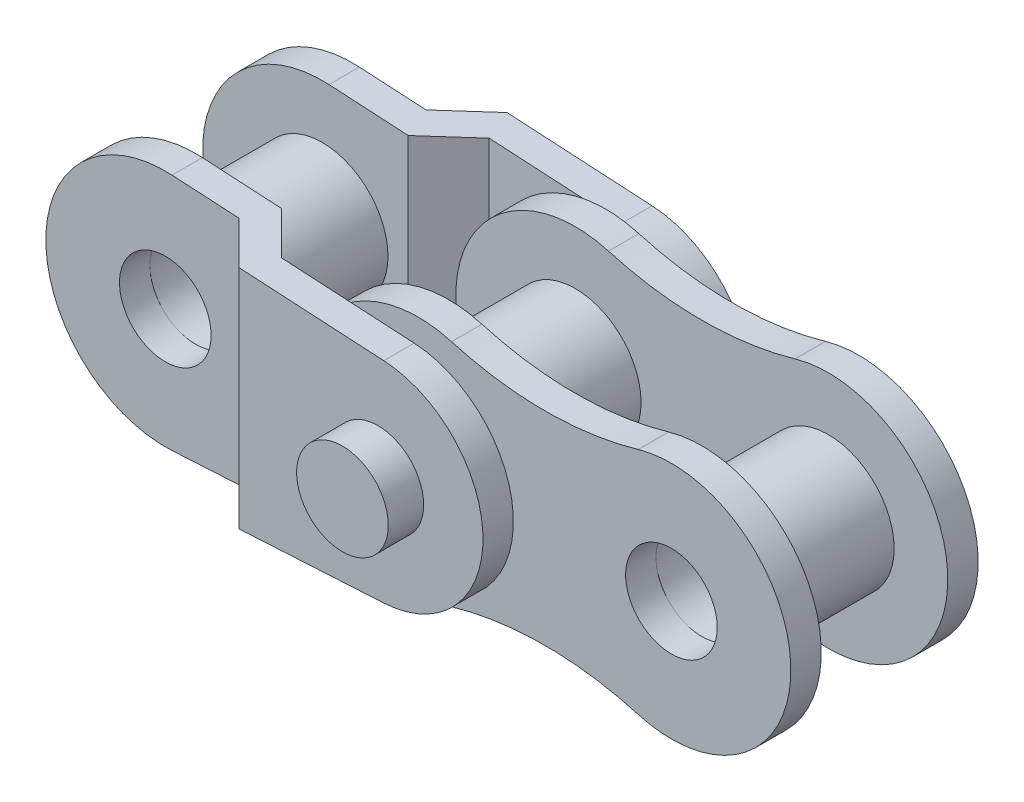
SolidWorks part; units mm, degrees
ref_plane "Front Plane" through (0, 0, 0) normal (0, 0, 1) x (1, 0, 0)
ref_plane "Top Plane" through (0, 0, 0) normal (0, 1, 0) x (1, 0, 0)
ref_plane "Right Plane" through (0, 0, 0) normal (1, 0, 0) x (0, 0, -1)
sketch "Sketch1" plane through (0, 0, 0) normal (0, 0, 1) x (1, 0, 0)
  line L0 (-3.175, 0) -> (3.175, 0) construction
  line L1 (-3.175, 2.9972) -> (-3.175, -2.9972) construction
  line L2 (0, -2.5476) -> (0, 2.5476) construction
  circle A0 centre (-3.175, 0) radius 1.651
  circle A1 centre (3.175, 0) radius 1.651
  circle A2 centre (-3.175, 0) radius 1.1493
  circle A3 centre (3.175, 0) radius 1.1493
  arc A4 (-2.3429, 2.8794) -> (-2.3429, -2.8794) centre (-3.175, 0) ccw
  arc A5 (2.3429, -2.8794) -> (2.3429, 2.8794) centre (3.175, 0) ccw
  arc A6 (-2.3429, 2.8794) -> (2.3429, 2.8794) centre (0, 10.9864) ccw
  arc A7 (-2.3429, -2.8794) -> (2.3429, -2.8794) centre (0, -10.9864) cw
  dimension "Roller Dia" = 3.302
  dimension "Pin Dia" = 2.2987
  dimension "Pitch" = 6.35
  dimension "H" = 5.9944
  dimension "D2" = 5.0952
sketch "Sketch2" plane through (0, 0, 0) normal (0, 1, 0) x (1, 0, 0)
  line L0 (0, 1.5875) -> (0, -1.5875) construction
  point P2 (0, -2.3495)
  point P4 (0, 2.3495)
  point P5 (0, 2.6035)
  point P6 (0, 3.3655)
  dimension "W" = 3.175
  dimension "T" = 0.762
  dimension "D1" = 0.762
  dimension "D2" = 0.762
  dimension "D3" = 0.254
ref_plane "Plane1" through (0, 0, 1.5875) normal (0, 0, 1) x (1, 0, 0)
ref_plane "Plane2" through (0, 0, -2.6035) normal (0, 0, 1) x (1, 0, 0)
sketch "Sketch5" plane through (0, 0, 1.5875) normal (0, 0, 1) x (1, 0, 0)
  arc A0 (-2.3429, 2.8794) -> (-2.3429, -2.8794) centre (-3.175, 0) ccw construction
  arc A1 (-2.3429, 2.8794) -> (2.3429, 2.8794) centre (0, 10.9864) ccw construction
  circle A2 centre (-3.175, 0) radius 1.1493 construction
  arc A3 (2.3429, -2.8794) -> (2.3429, 2.8794) centre (3.175, 0) ccw construction
  circle A4 centre (3.175, 0) radius 1.1493 construction
  arc A5 (2.3429, -2.8794) -> (-2.3429, -2.8794) centre (0, -10.9864) ccw construction
  arc A6 (-2.3429, 2.8794) -> (-2.3429, -2.8794) centre (-3.175, 0) ccw
  arc A7 (-2.3429, 2.8794) -> (2.3429, 2.8794) centre (0, 10.9864) ccw
  circle A8 centre (-3.175, 0) radius 1.1493
  arc A9 (2.3429, -2.8794) -> (2.3429, 2.8794) centre (3.175, 0) ccw
  circle A10 centre (3.175, 0) radius 1.1493
  arc A11 (2.3429, -2.8794) -> (-2.3429, -2.8794) centre (0, -10.9864) ccw
sketch "Sketch7" plane through (0, 0, -2.6035) normal (0, 0, 1) x (1, 0, 0)
  line L0 (3.175, 2.6375) -> (3.175, -2.6375) construction
  circle A0 centre (3.175, 0) radius 2.6375
  circle A1 centre (-3.175, 0) radius 1.1493 construction
  arc A2 (2.3429, -2.8794) -> (2.3429, 2.8794) centre (3.175, 0) ccw construction
  circle A8 centre (3.175, 0) radius 1.1493
  dimension "D2" = 5.2751
sketch "Sketch4" plane through (0, 0, 0) normal (0, 0, 1) x (1, 0, 0)
  circle A0 centre (-3.175, 0) radius 1.651 construction
  circle A1 centre (-3.175, 0) radius 1.651
  circle A2 centre (3.175, 0) radius 1.651 construction
  circle A3 centre (3.175, 0) radius 1.651 construction
  circle A4 centre (-3.175, 0) radius 1.1747
  circle A5 centre (3.175, 0) radius 1.1747 construction
  dimension "D1" = 2.3495
  dimension "D2" = 2.3495
extrude "Boss-Extrude1" add sketch "Sketch4" along normal mid plane 3.175
pattern_linear "LPattern1" count 3 spacing 6.35 along (1, 0, 0) of bodies 101
sketch "Sketch8" plane through (0, 0, 0) normal (0, 0, 1) x (1, 0, 0)
  circle A0 centre (3.175, 0) radius 1.1493
  circle A2 centre (3.175, 0) radius 1.1493 construction
extrude "Boss-Extrude4" add sketch "Sketch8" against normal mid plane 8.509 separate body
sketch "Sketch15" plane through (0, 0, 1.5875) normal (0, 0, 1) x (1, 0, 0)
  arc A0 (-2.3429, 2.8794) -> (-2.3429, -2.8794) centre (-3.175, 0) ccw construction
  arc A1 (-2.3429, 2.8794) -> (2.3429, 2.8794) centre (0, 10.9864) ccw construction
  arc A2 (2.3429, -2.8794) -> (2.3429, 2.8794) centre (3.175, 0) ccw construction
  arc A3 (2.3429, -2.8794) -> (-2.3429, -2.8794) centre (0, -10.9864) ccw construction
  circle A4 centre (-3.175, 0) radius 1.1493 construction
  circle A5 centre (3.175, 0) radius 1.1493 construction
  arc A6 (-2.3429, 2.8794) -> (-2.3429, -2.8794) centre (-3.175, 0) ccw
  arc A7 (-2.3429, 2.8794) -> (2.3429, 2.8794) centre (0, 10.9864) ccw
  arc A8 (2.3429, -2.8794) -> (2.3429, 2.8794) centre (3.175, 0) ccw
  arc A9 (2.3429, -2.8794) -> (-2.3429, -2.8794) centre (0, -10.9864) ccw
  circle A10 centre (-3.175, 0) radius 1.1493
  circle A11 centre (3.175, 0) radius 1.1493
extrude "Boss-Extrude6" add sketch "Sketch15" along normal blind 0.762 separate body
mirror "Mirror3" about plane through (0, 0, 0) normal (0, 0, 1) of bodies 127
move or copy body "Body-Move/Copy1" bodies to move or copy 129 127 copy no translate (6.35, 0, 0)
sketch "Sketch9" plane through (0, 0, 0) normal (0, 0, 1) x (1, 0, 0)
  line L0 (-3.0052, 2.9924) -> (3.3244, 2.6333)
  line L1 (-3.0052, -2.9924) -> (3.3244, -2.6333)
  arc A0 (-2.3429, 2.8794) -> (-2.3429, -2.8794) centre (-3.175, 0) ccw construction
  circle A1 centre (3.175, 0) radius 2.6375 construction
  arc A2 (-3.0052, 2.9924) -> (-3.0052, -2.9924) centre (-3.175, 0) ccw
  arc A3 (3.3244, -2.6333) -> (3.3244, 2.6333) centre (3.175, 0) ccw
  circle A4 centre (-3.175, 0) radius 1.1493 construction
  circle A5 centre (3.175, 0) radius 1.1493 construction
  circle A6 centre (-3.175, 0) radius 1.1493
  circle A7 centre (3.175, 0) radius 1.1493
extrude "Boss-Extrude5" add sketch "Sketch9" against normal up to vertex (3.3655 mm away) separate body up to point (0, 0, -3.3655)
sketch "Sketch10" plane through (0, 0, 0) normal (0, 1, 0) x (1, 0, 0)
  line L0 (-6.1722, 2.3495) -> (-1.3316, 2.3495)
  line L1 (-1.3316, 2.3495) -> (-0.3156, 3.3655)
  line L2 (-0.3156, 3.3655) -> (-6.1722, 3.3655)
  line L3 (-6.1722, 3.3655) -> (-6.1722, 2.3495)
  line L4 (-6.1722, 3.3655) -> (-6.1722, 0) construction
  line L5 (-3.0052, 3.3655) -> (-6.1722, 3.3655) construction
  line L6 (3.3244, 3.3655) -> (-3.0052, 3.3655) construction
  line L7 (-3.175, -1.5875) -> (-3.175, 2.3495) construction
  line L8 (-4.3243, -1.5875) -> (-2.0257, -1.5875) construction
  line L9 (3.175, 2.6035) -> (3.175, 4.2545) construction
  line L10 (2.0257, 2.6035) -> (4.3243, 2.6035) construction
  line L11 (4.3243, 4.2545) -> (2.0257, 4.2545) construction
  line L12 (-6.1722, 1.5875) -> (-1.016, 1.5875)
  line L13 (-1.016, 1.5875) -> (0, 2.6035)
  line L14 (0, 2.6035) -> (6.1722, 2.6035)
  line L15 (6.1722, 2.6035) -> (6.1722, 0)
  line L16 (6.1722, 0) -> (-6.1722, 0)
  line L17 (-6.1722, 0) -> (-6.1722, 1.5875)
  line L18 (0.5375, 2.6035) -> (5.8125, 2.6035) construction
  line L19 (-0.8236, 2.8575) -> (-0.2848, 2.3187) construction
  line L20 (-6.1722, 2.3495) -> (-6.1722, 1.5875) construction
  line L21 (0, 1.5875) -> (0, -1.5875) construction
  line L22 (6.1722, -1.5875) -> (6.1722, 0) construction
  dimension "D1" = 45
extrude "Cut-Extrude1" cut sketch "Sketch10" against normal through all and the other way through all
mirror "Mirror1" about plane through (0, 0, 0) normal (0, 0, 1) of bodies 121
equation "\"D2@Sketch1\" =\"H@Sketch1\"*.85"
equation "\"D1@Sketch2\" = \"T@Sketch2\""
equation "\"D1@Sketch4\" = \"Pin Dia@Sketch1\"+.002"
equation "\"D2@Sketch4\" = \"D1@Sketch4\""
equation "\"D1@Boss-Extrude1\" = \"W@Sketch2\""
equation "\"D2@Sketch2\" = \"T@Sketch2\""
equation "\"D2@Sketch7\" = \"H@Sketch1\"*.88"
equation "\"D3@LPattern1\" = \"Pitch@Sketch1\""
equation "\"D1@Boss-Extrude6\" = \"T@Sketch2\""
